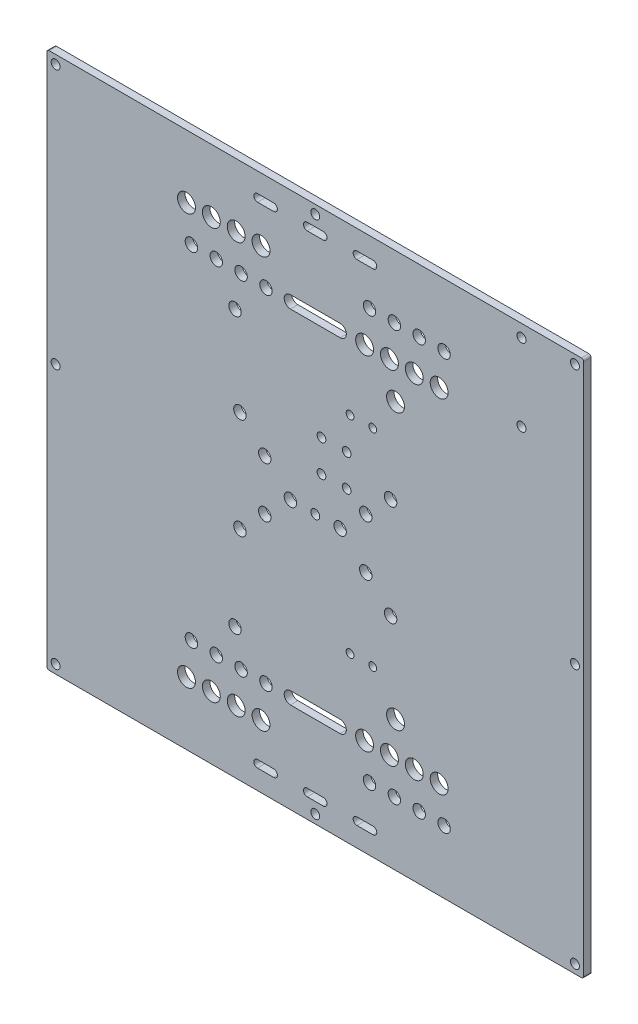
SolidWorks part; units mm, degrees
material "6063-T6"
ref_plane "Front" through (0, 0, 0) normal (0, 0, 1) x (1, 0, 0)
ref_plane "Top" through (0, 0, 0) normal (0, 1, 0) x (1, 0, 0)
ref_plane "Right" through (0, 0, 0) normal (1, 0, 0) x (0, 0, -1)
sketch "Sketch1" plane through (0, 0, 0) normal (0, 0, 1) x (1, 0, 0)
  line L0 (-108, -107.125) -> (-107.125, -108) construction
  line L1 (-107.125, -108) -> (107.125, -108)
  line L2 (-108, -107.125) -> (-108, 107.125)
  line L3 (-107.125, 108) -> (107.125, 108)
  line L4 (108, -107.125) -> (108, 107.125)
  line L5 (-107.7437, -107.7437) -> (107.7437, 107.7437) construction
  line L6 (-107.7437, 107.7437) -> (107.7437, -107.7437) construction
  line L7 (-107.125, 108) -> (-108, 107.125) construction
  line L8 (107.125, 108) -> (108, 107.125) construction
  line L9 (108, -107.125) -> (107.125, -108) construction
  line L10 (0, -108) -> (0, 108) construction
  line L11 (-108, 0) -> (108, 0) construction
  line L12 (-108, -69) -> (108, -69) construction
  line L13 (-108, -82.65) -> (108, -82.65) construction
  line L14 (-104.5, -104.5) -> (104.5, -104.5) construction
  line L15 (-104.5, 104.5) -> (-104.5, -104.5) construction
  line L16 (-3.25, -98.62) -> (3.25, -98.62) construction
  line L17 (-3.25, -97.12) -> (3.25, -97.12)
  line L18 (-3.25, -100.12) -> (3.25, -100.12)
  line L19 (-23.25, -98.62) -> (-16.75, -98.62) construction
  line L20 (-23.25, -97.12) -> (-16.75, -97.12)
  line L21 (-23.25, -100.12) -> (-16.75, -100.12)
  line L22 (23.25, -98.62) -> (16.75, -98.62) construction
  line L23 (23.25, -97.12) -> (16.75, -97.12)
  line L24 (23.25, -100.12) -> (16.75, -100.12)
  line L25 (-3.25, 98.62) -> (3.25, 98.62) construction
  line L26 (-3.25, 97.12) -> (3.25, 97.12)
  line L27 (-3.25, 100.12) -> (3.25, 100.12)
  line L28 (23.25, 98.62) -> (16.75, 98.62) construction
  line L29 (23.25, 97.12) -> (16.75, 97.12)
  line L30 (23.25, 100.12) -> (16.75, 100.12)
  line L31 (-23.25, 98.62) -> (-16.75, 98.62) construction
  line L32 (-23.25, 97.12) -> (-16.75, 97.12)
  line L33 (-23.25, 100.12) -> (-16.75, 100.12)
  line L34 (-10, -69) -> (10, -69) construction
  line L35 (-10, -66.5) -> (10, -66.5)
  line L36 (-10, -71.5) -> (10, -71.5)
  line L37 (-10, 69) -> (10, 69) construction
  line L38 (-10, 71.5) -> (10, 71.5)
  line L39 (-10, 66.5) -> (10, 66.5)
  line L40 (83, 108) -> (83, -108) construction
  line L41 (108, -55.35) -> (-108, -55.35) construction
  line L42 (-108, -41.57) -> (108, -41.57) construction
  line L43 (12.64, 15.17) -> (2.5, 15.17) construction
  line L44 (2.5, 15.17) -> (2.5, 28) construction
  line L45 (2.5, 28) -> (12.64, 28) construction
  line L46 (12.64, 28) -> (12.64, 15.17) construction
  arc A0 (-107.125, 108) -> (-108, 107.125) centre (-107.125, 107.125) ccw
  arc A1 (108, 107.125) -> (107.125, 108) centre (107.125, 107.125) ccw
  arc A2 (107.125, -108) -> (108, -107.125) centre (107.125, -107.125) ccw
  arc A3 (-108, -107.125) -> (-107.125, -108) centre (-107.125, -107.125) ccw
  circle A4 centre (-104.5, -104.5) radius 1.8
  circle A5 centre (104.5, -104.5) radius 1.8
  circle A6 centre (-104.5, 104.5) radius 1.8
  circle A7 centre (104.5, 104.5) radius 1.8
  circle A8 centre (-49.85, -69) radius 2.5
  circle A9 centre (-39.85, -69) radius 2.5
  circle A10 centre (-29.85, -69) radius 2.5
  circle A11 centre (-19.855, -69) radius 2.5
  circle A12 centre (49.85, -69) radius 3.6
  circle A13 centre (39.85, -69) radius 3.6
  circle A14 centre (29.85, -69) radius 3.6
  circle A15 centre (19.855, -69) radius 3.6
  circle A16 centre (0, -104.5) radius 1.8
  circle A17 centre (0, 104.5) radius 1.8
  circle A18 centre (49.85, 69) radius 3.6
  circle A19 centre (39.85, 69) radius 3.6
  circle A20 centre (29.85, 69) radius 3.6
  circle A21 centre (19.855, 69) radius 3.6
  circle A22 centre (-19.855, 69) radius 2.5
  circle A23 centre (-29.85, 69) radius 2.5
  circle A24 centre (-39.85, 69) radius 2.5
  circle A25 centre (-49.85, 69) radius 2.5
  circle A26 centre (-104.5, 0) radius 1.8
  circle A27 centre (104.5, 0) radius 1.8
  circle A28 centre (-51.83, -82.65) radius 3.6
  circle A29 centre (-41.83, -82.65) radius 3.6
  circle A30 centre (-31.83, -82.65) radius 3.6
  circle A31 centre (-21.835, -82.65) radius 3.6
  circle A32 centre (51.83, -82.65) radius 2.5
  circle A33 centre (41.83, -82.65) radius 2.5
  circle A34 centre (31.83, -82.65) radius 2.5
  circle A35 centre (21.835, -82.65) radius 2.5
  circle A36 centre (-51.83, 82.65) radius 3.6
  circle A37 centre (-41.83, 82.65) radius 3.6
  circle A38 centre (-31.83, 82.65) radius 3.6
  circle A39 centre (-21.835, 82.65) radius 3.6
  circle A40 centre (51.83, 82.65) radius 2.5
  circle A41 centre (41.83, 82.65) radius 2.5
  circle A42 centre (31.83, 82.65) radius 2.5
  circle A43 centre (21.835, 82.65) radius 2.5
  arc A44 (-3.25, -97.12) -> (-3.25, -100.12) centre (-3.25, -98.62) ccw
  arc A45 (3.25, -100.12) -> (3.25, -97.12) centre (3.25, -98.62) ccw
  arc A46 (-23.25, -97.12) -> (-23.25, -100.12) centre (-23.25, -98.62) ccw
  arc A47 (-16.75, -100.12) -> (-16.75, -97.12) centre (-16.75, -98.62) ccw
  arc A48 (23.25, -97.12) -> (23.25, -100.12) centre (23.25, -98.62) cw
  arc A49 (16.75, -100.12) -> (16.75, -97.12) centre (16.75, -98.62) cw
  arc A50 (-3.25, 97.12) -> (-3.25, 100.12) centre (-3.25, 98.62) cw
  arc A51 (3.25, 100.12) -> (3.25, 97.12) centre (3.25, 98.62) cw
  arc A52 (23.25, 97.12) -> (23.25, 100.12) centre (23.25, 98.62) ccw
  arc A53 (16.75, 100.12) -> (16.75, 97.12) centre (16.75, 98.62) ccw
  arc A54 (-23.25, 97.12) -> (-23.25, 100.12) centre (-23.25, 98.62) cw
  arc A55 (-16.75, 100.12) -> (-16.75, 97.12) centre (-16.75, 98.62) cw
  arc A56 (-10, -66.5) -> (-10, -71.5) centre (-10, -69) ccw
  arc A57 (10, -71.5) -> (10, -66.5) centre (10, -69) ccw
  arc A58 (-10, 71.5) -> (-10, 66.5) centre (-10, 69) ccw
  arc A59 (10, 66.5) -> (10, 71.5) centre (10, 69) ccw
  circle A60 centre (83, 103) radius 1.8
  circle A61 centre (83, 72) radius 1.8
  circle A62 centre (-32.3, -55.35) radius 2.5
  circle A63 centre (32.3, -55.35) radius 3.6
  circle A64 centre (32.3, 55.35) radius 3.6
  circle A65 centre (-32.3, 55.35) radius 2.5
  circle A66 centre (14, -41.57) radius 1.57
  circle A67 centre (23.12, -41.57) radius 1.57
  circle A68 centre (23.12, 41.57) radius 1.57
  circle A69 centre (14, 41.57) radius 1.57
  circle A70 centre (0, 0) radius 1.8
  circle A71 centre (-10, 0) radius 2.5
  circle A72 centre (10, 0) radius 2.5
  circle A73 centre (-20.32, 10.16) radius 2.5
  circle A74 centre (-30.32, 20.32) radius 2.5
  circle A75 centre (30.32, 20.32) radius 2.5
  circle A76 centre (20.32, 10.16) radius 2.5
  circle A77 centre (30.32, -20.32) radius 2.5
  circle A78 centre (20.32, -10.16) radius 2.5
  circle A79 centre (-20.32, -10.16) radius 2.5
  circle A80 centre (-30.32, -20.32) radius 2.5
  circle A81 centre (2.5, 28) radius 1.75
  circle A82 centre (12.64, 28) radius 1.75
  circle A83 centre (2.5, 15.17) radius 1.75
  circle A84 centre (12.64, 15.17) radius 1.75
  point P0 (0, 0)
  point P14 (-107.5625, -107.5625)
  point P16 (-107.5625, 107.5625)
  point P18 (107.5625, 107.5625)
  point P21 (107.5625, -107.5625)
  point P112 (0, -98.62)
  point P119 (-20, -98.62)
  point P126 (20, -98.62)
  point P133 (0, 98.62)
  point P140 (20, 98.62)
  point P147 (-20, 98.62)
  point P154 (0, -69)
  point P161 (0, 69)
  dimension "D1" = 1.75
  dimension "D3" = 3.6
  dimension "D4" = 3.5
  dimension "D7" = 5
  dimension "D9" = 7.2
  dimension "D17" = 3
  dimension "D18" = 9.5
  dimension "D20" = 10.5
  dimension "D22" = 25
  dimension "D24" = 25
  dimension "D26" = 3.2
  dimension "D27" = 27.4
  dimension "D28" = 75.7
  dimension "D29" = 52.65
  dimension "D31" = 3.14
  dimension "D35" = 10.32
  dimension "D34" = 10
  dimension "D39" = 3.5
  dimension "D40" = 12.83
  dimension "D2" = 216
  dimension "D5" = 39
  dimension "D6" = 25.35
  dimension "D8" = 39.71
  dimension "D10" = 59.7
  dimension "D11" = 79.7
  dimension "D12" = 99.7
  dimension "D13" = 1.98
  dimension "D14" = 1.98
  dimension "D15" = 1.98
  dimension "D16" = 1.98
  dimension "D19" = 9.38
  dimension "D21" = 5
  dimension "D23" = 5
  dimension "D25" = 25
  dimension "D30" = 66.43
  dimension "D32" = 9.12
  dimension "D33" = 14
  dimension "D36" = 10
  dimension "D37" = 10.16
  dimension "D38" = 20.32
  dimension "D41" = 15.17
  dimension "D42" = 2.5
  dimension "D43" = 10.14
extrude "Boss-Extrude1" add sketch "Sketch1" along normal blind 3
